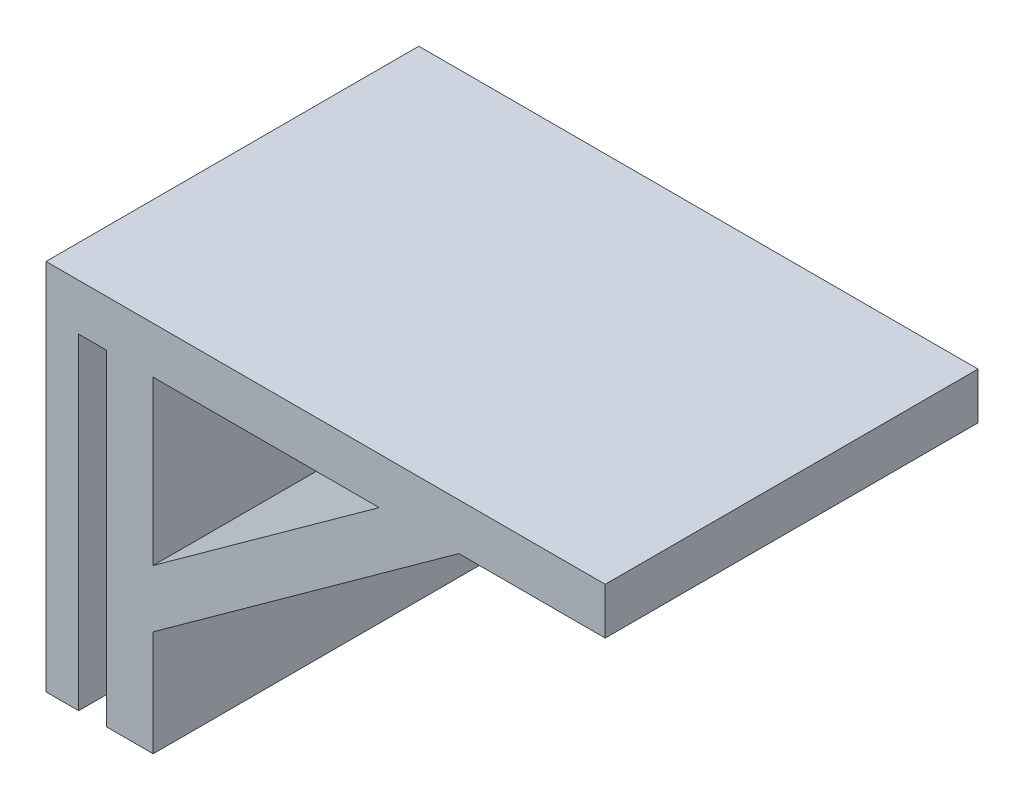
SolidWorks part; units mm, degrees
ref_plane "Plan de face" through (0, 0, 0) normal (0, 0, 1) x (1, 0, 0)
ref_plane "Plan de dessus" through (0, 0, 0) normal (0, 1, 0) x (1, 0, 0)
ref_plane "Plan de droite" through (0, 0, 0) normal (1, 0, 0) x (0, 0, -1)
sketch "Esquisse1" plane through (0, 0, 0) normal (0, 0, 1) x (1, 0, 0)
  line L0 (0, 0) -> (0, 80)
  line L1 (0, 80) -> (120, 80)
  line L2 (120, 80) -> (120, 70)
  line L3 (120, 70) -> (23, 70)
  line L4 (23, 70) -> (23, 0)
  line L5 (0, 0) -> (7, 0)
  line L6 (7, 0) -> (7, 70)
  line L7 (7, 70) -> (13, 70)
  line L8 (13, 70) -> (13, 0)
  line L9 (13, 0) -> (23, 0)
  line L10 (23, 30.8907) -> (63.8097, 70)
  line L11 (63.8097, 70) -> (73.7287, 70)
  line L12 (73.7287, 70) -> (23, 21.385)
  dimension "D1" = 10
  dimension "D2" = 70
  dimension "D3" = 70
  dimension "D5" = 6
  dimension "D6" = 7
  dimension "D7" = 10
  dimension "D8" = 120
extrude "Boss.-Extru.1" add sketch "Esquisse1" along normal blind 80 contours L9 L4 L3 L2 L1 L0 L5 L6 L7 L8
sketch "Esquisse2" plane through (0, 0, 0) normal (0, 0, -1) x (-1, 0, 0)
  line L0 (-71.5, 70) -> (-23, 35)
  line L1 (-120, 70) -> (-23, 70) construction
  line L2 (-23, 70) -> (-23, 0) construction
  line L3 (-23, 35) -> (-23, 22.668)
  line L4 (-23, 22.668) -> (-88.5886, 70)
  line L5 (-88.5886, 70) -> (-71.5, 70)
  dimension "D1" = 10
extrude "Boss.-Extru.3" add sketch "Esquisse2" against normal blind 80
